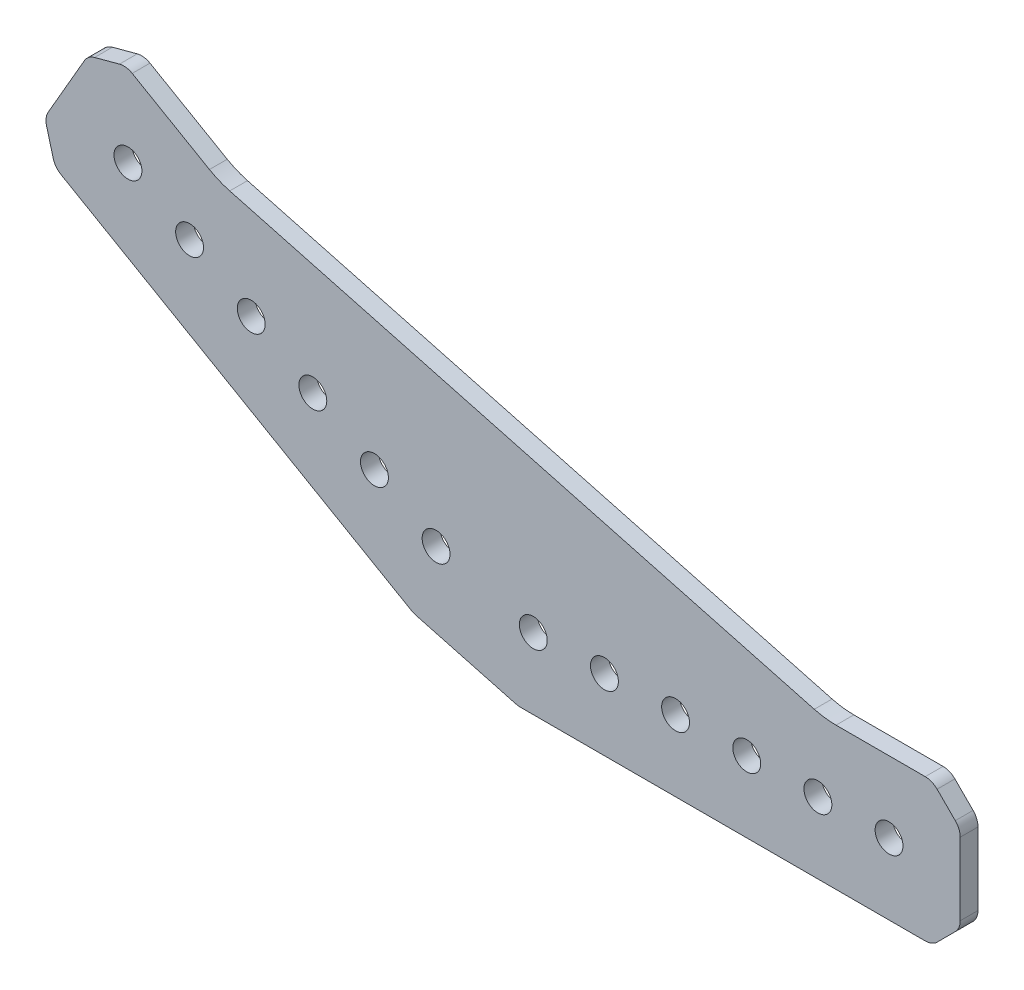
SolidWorks part; units mm, degrees
material "5052-H32"
ref_plane "Front Plane" through (0, 0, 0) normal (0, 0, 1) x (1, 0, 0)
ref_plane "Top Plane" through (0, 0, 0) normal (0, 1, 0) x (1, 0, 0)
ref_plane "Right Plane" through (0, 0, 0) normal (1, 0, 0) x (0, 0, -1)
ref_plane "Plane4" through (0, 0, 0) normal (0, 0, -1) x (-1, 0, 0)
sketch "Sketch1" plane through (0, 0, 0) normal (0, 0, -1) x (-1, 0, 0)
  line L0 (-82.6574, 0) -> (-10.395, 0)
  line L1 (-9.6185, 0.1022) -> (8.2788, 4.8978)
  line L2 (9.0023, 5.1975) -> (71.5834, 41.3287)
  line L3 (72.9812, 43.1503) -> (74.168, 47.5798)
  line L4 (73.8683, 49.8563) -> (67.411, 61.0408)
  line L5 (65.5894, 62.4385) -> (61.1598, 63.6254)
  line L6 (58.8834, 63.3257) -> (45.0953, 55.3652)
  line L7 (41.4776, 53.8667) -> (-62.854, 25.9111)
  line L8 (-66.7362, 25.4) -> (-82.6574, 25.4)
  line L9 (-84.7787, 24.5213) -> (-88.0213, 21.2787)
  line L10 (-88.9, 19.1574) -> (-88.9, 6.2426)
  line L11 (-88.0213, 4.1213) -> (-84.7787, 0.8787)
  circle A0 centre (-12.7, 12.7) radius 2.4892
  circle A1 centre (4.6485, 17.3485) radius 2.4892
  circle A2 centre (-63.5, 12.7) radius 2.4892
  circle A3 centre (-38.1, 12.7) radius 2.4892
  circle A4 centre (26.6456, 30.0485) radius 2.4892
  circle A5 centre (48.6426, 42.7485) radius 2.4892
  circle A6 centre (-76.2, 12.7) radius 2.4892
  circle A7 centre (-50.8, 12.7) radius 2.4892
  circle A8 centre (-25.4, 12.7) radius 2.4892
  circle A9 centre (15.647, 23.6985) radius 2.4892
  circle A10 centre (37.6441, 36.3985) radius 2.4892
  circle A11 centre (59.6411, 49.0985) radius 2.4892
  arc A12 (-10.395, 0) -> (-9.6185, 0.1022) centre (-10.395, 3) ccw
  arc A13 (8.2788, 4.8978) -> (9.0023, 5.1975) centre (7.5023, 7.7956) ccw
  arc A14 (71.5834, 41.3287) -> (72.9812, 43.1503) centre (70.0834, 43.9268) ccw
  arc A15 (74.168, 47.5798) -> (73.8683, 49.8563) centre (71.2703, 48.3563) ccw
  arc A16 (67.411, 61.0408) -> (65.5894, 62.4385) centre (64.8129, 59.5408) ccw
  arc A17 (61.1598, 63.6254) -> (58.8834, 63.3257) centre (60.3834, 60.7276) ccw
  arc A18 (45.0953, 55.3652) -> (41.4776, 53.8667) centre (37.5953, 68.3555) cw
  arc A19 (-62.854, 25.9111) -> (-66.7362, 25.4) centre (-66.7362, 40.4) cw
  arc A20 (-82.6574, 25.4) -> (-84.7787, 24.5213) centre (-82.6574, 22.4) ccw
  arc A21 (-88.0213, 21.2787) -> (-88.9, 19.1574) centre (-85.9, 19.1574) ccw
  arc A22 (-88.9, 6.2426) -> (-88.0213, 4.1213) centre (-85.9, 6.2426) ccw
  arc A23 (-84.7787, 0.8787) -> (-82.6574, 0) centre (-82.6574, 3) ccw
extrude "Boss-Extrude1" add sketch "Sketch1" against normal blind 3.175
